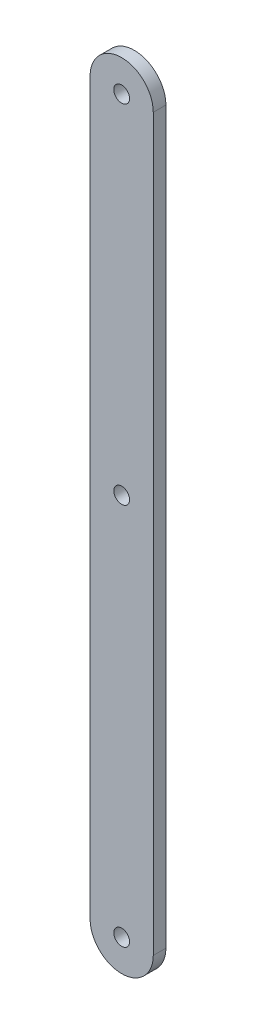
SolidWorks part; units mm, degrees
material "1060 Alloy"
ref_plane "Front Plane" through (0, 0, 0) normal (0, 0, 1) x (1, 0, 0)
ref_plane "Top Plane" through (0, 0, 0) normal (0, 1, 0) x (1, 0, 0)
ref_plane "Right Plane" through (0, 0, 0) normal (1, 0, 0) x (0, 0, -1)
sketch "Sketch1" plane through (0, 0, 0) normal (0, 0, 1) x (1, 0, 0)
  line L0 (0, 0) -> (0, 146.812) construction
  line L1 (-6.35, 0) -> (-6.35, 146.812)
  line L2 (6.35, 0) -> (6.35, 146.812)
  arc A0 (-6.35, 0) -> (6.35, 0) centre (0, 0) ccw
  arc A1 (6.35, 146.812) -> (-6.35, 146.812) centre (0, 146.812) ccw
  circle A2 centre (0, 0) radius 1.5875
  circle A3 centre (0, 76.962) radius 1.5875
  circle A4 centre (0, 146.812) radius 1.5875
  point P3 (0, 73.406)
  dimension "D2" = 6.35
  dimension "D3" = 3.175
  dimension "D4" = 76.962
  dimension "D1" = 69.85
extrude "Boss-Extrude1" add sketch "Sketch1" along normal blind 2.54
